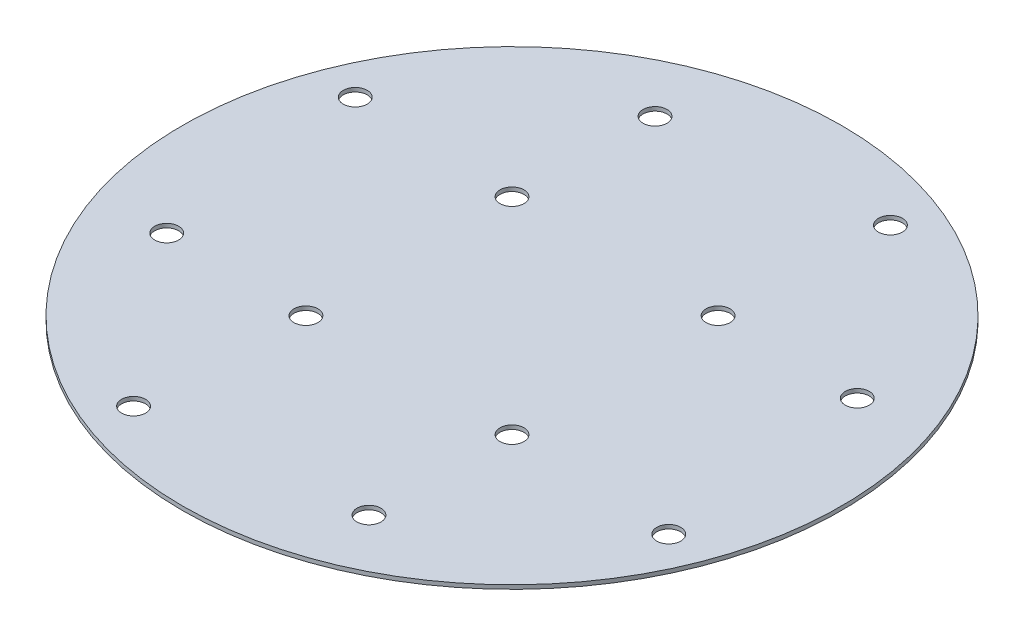
SolidWorks part; units mm, degrees
material "6061-T6 (SS)"
ref_plane "Front Plane" through (0, 0, 0) normal (0, 0, 1) x (1, 0, 0)
ref_plane "Top Plane" through (0, 0, 0) normal (0, 1, 0) x (1, 0, 0)
ref_plane "Right Plane" through (0, 0, 0) normal (1, 0, 0) x (0, 0, -1)
sketch "Sketch2" plane through (0, 0, 0) normal (1, 0, 0) x (0, 0, -1)
  line L0 (0, 0) -> (-82.55, 0)
  line L1 (-82.55, 0) -> (-82.55, 1)
  line L2 (-82.55, 1) -> (0, 1)
  line L5 (0, 1) -> (0, 0)
  dimension "D1" = 82.55
  dimension "D2" = 1
ref_axis "Axis1" through (0, -0.05, 0) along (0, 1, 0)
revolve "Revolve1" add sketch "Sketch2" angle 360 about axis through (0, -0.05, 0) along (0, 1, 0)
hole_wizard "#10 (0.1935) Diameter Hole1" positions "Sketch6" profile "Sketch7" hole size "#10" standard "ANSI Inch" end condition through all
sketch "Sketch6" plane through (0, 1, 0) normal (0, 1, 0) x (1, 0, 0)
  line L0 (0, 0) -> (-53.438, 129.0108) construction
  line L2 (0, 0) -> (0, 109.0908) construction
  line L3 (0, 0) -> (-76.2663, 31.5905) construction
  line L4 (0, 0) -> (-47.7784, 47.7784) construction
  circle A0 centre (0, 0) radius 82.55 construction
  point P0 (-25.3336, 61.1608)
  point P11 (264.7437, 73.7878)
  point P20 (-67.0275, 27.7637)
  point P22 (-25.8094, 25.8094)
  dimension "D1" = 22.5
  dimension "D2" = 66.2
  dimension "D3" = 72.55
  dimension "D4" = 45
  dimension "D6" = 22.5
  dimension "D5" = 36.5
sketch "Sketch7" plane through (-25.3336, 1, -61.1608) normal (1, 0, 0) x (0, 0, 1)
  line L0 (0, 0) -> (0, 1)
  line L1 (0, 1) -> (3, 1)
  line L2 (3, 1) -> (3, 0)
  line L5 (3, 0) -> (0, 0)
  line L11 (0, -6.35) -> (0, 107.95) construction
  dimension "Thru Hole Dia." = 6
  dimension "Thru Hole Depth" = 1
pattern_circular "CirPattern3" count 4 over 360 about axis through (0, 0, 0) along (0, 1, 0) of "#10 (0.1935) Diameter Hole1"
equation "\"TubeDiameter\" = 6.500in"
equation "\"D1@Sketch2\"=\"TubeDiameter\"/2"
equation "\"D2@Sketch6\"=66.2"
equation "\"D3@Sketch6\"=\"TubeDiameter\"/2-10mm"
